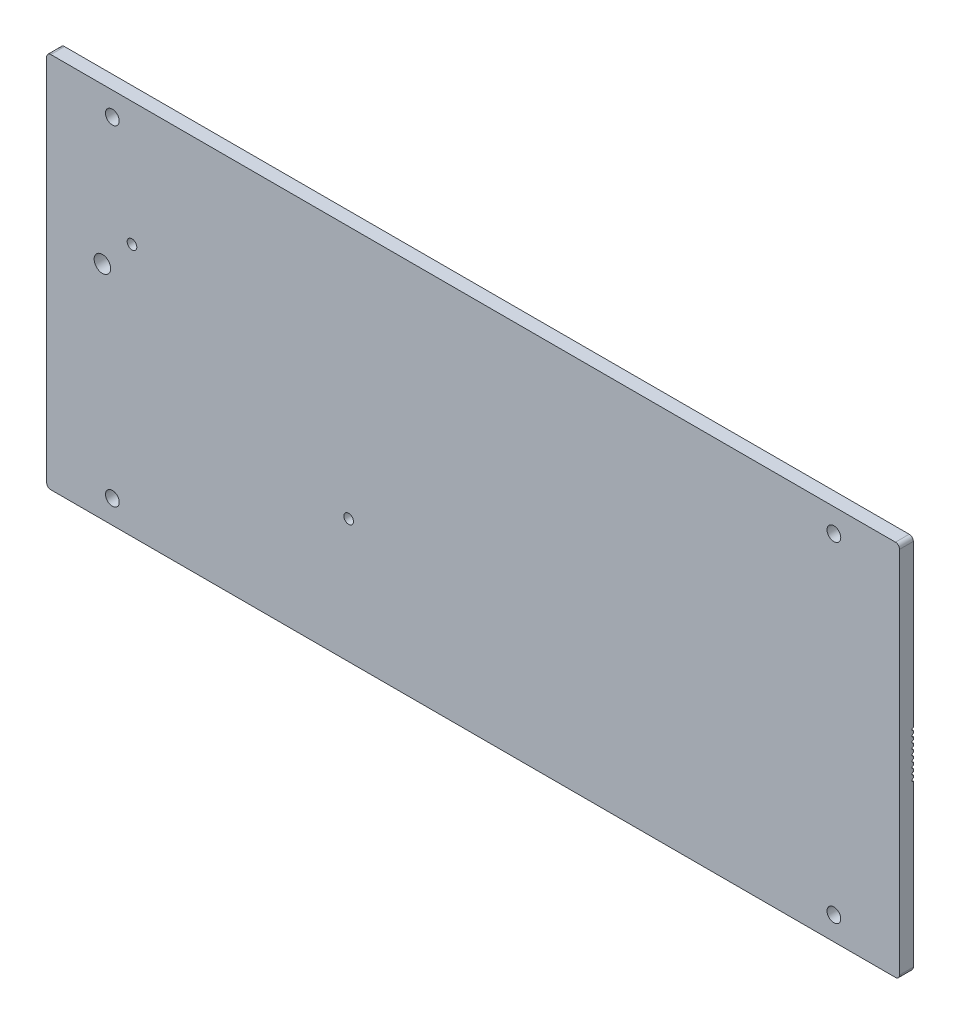
SolidWorks part; units mm, degrees
material "Alliage 1060"
ref_plane "Plan de face" through (0, 0, 0) normal (0, 0, 1) x (1, 0, 0)
ref_plane "Plan de dessus" through (0, 0, 0) normal (0, 1, 0) x (1, 0, 0)
ref_plane "Plan de droite" through (0, 0, 0) normal (1, 0, 0) x (0, 0, -1)
sketch "Esquisse1" plane through (0, 0, 0) normal (0, 0, 1) x (1, 0, 0)
  line L1 (-153.5, -68.5) -> (153.5, -68.5)
  line L2 (-155, -67) -> (-155, 67)
  line L3 (-153.5, 68.5) -> (153.5, 68.5)
  line L4 (155, -67) -> (155, 67)
  line L5 (-155, -68.5) -> (155, 68.5) construction
  line L6 (-155, 68.5) -> (155, -68.5) construction
  arc A0 (-153.5, -68.5) -> (-155, -67) centre (-153.5, -67) cw
  arc A1 (153.5, -68.5) -> (155, -67) centre (153.5, -67) ccw
  arc A2 (153.5, 68.5) -> (155, 67) centre (153.5, 67) cw
  arc A3 (-155, 67) -> (-153.5, 68.5) centre (-153.5, 67) cw
  point P0 (0, 0)
  dimension "D3" = 1.5
  dimension "D1" = 310
  dimension "D2" = 137
extrude "Boss.-Extru.1" add sketch "Esquisse1" along normal blind 5
ref_plane "Plan1" through (0, 0, 0) normal (0, -1, 0) x (-1, 0, 0)
sketch "Esquisse2" plane through (0, 0, 0) normal (0, 0, -1) x (-1, 0, 0)
  line L0 (-131.1192, -70) -> (-131.1192, -50) construction
  line L1 (-150, -70) -> (150, -70) construction
  line L2 (-155, 0) -> (155, 0) construction
  line L3 (-155, -67) -> (-155, 67) construction
  line L4 (155, 67) -> (155, -67) construction
  line L5 (0, 0) -> (0, 70) construction
  line L6 (-150, 70) -> (150, 70) construction
  circle A0 centre (-131.1192, -60) radius 2.5
  circle A1 centre (-131.1192, 60) radius 2.5
  circle A2 centre (131.1192, 60) radius 2.5
  circle A3 centre (131.1192, -60) radius 2.5
  dimension "D1" = 20
extrude "Enlèv. mat.-Extru.1" cut sketch "Esquisse2" against normal blind 5
sketch "Esquisse3" plane through (155, 0, 0) normal (1, 0, 0) x (0, 0, -1)
  circle A0 centre (0, 0) radius 0.5
  circle A1 centre (0, 2) radius 0.5
  circle A2 centre (0, 4) radius 0.5
  circle A3 centre (0, 6) radius 0.5
  circle A4 centre (0, 8) radius 0.5
  circle A5 centre (0, -2) radius 0.5
  circle A6 centre (0, -4) radius 0.5
  circle A7 centre (0, -6) radius 0.5
  circle A8 centre (0, -8) radius 0.5
  dimension "D1" = 5
  dimension "D2" = 5
extrude "Enlèv. mat.-Extru.2" cut sketch "Esquisse3" against normal through all both and the other way through all
sketch "Esquisse4" plane through (0, 0, 0) normal (0, 0, -1) x (-1, 0, 0)
  circle A0 centre (45.2359, -23.5) radius 1.75
  circle A1 centre (123.9859, 23.5) radius 1.75
extrude "Enlèv. mat.-Extru.3" cut sketch "Esquisse4" against normal blind 5
sketch "Esquisse6" plane through (0, 0, 0) normal (0, 0, -1) x (-1, 0, 0)
  circle A0 centre (134.7465, 11.9777) radius 3
extrude "Enlèv. mat.-Extru.4" cut sketch "Esquisse6" against normal blind 5
fillet "Congé1" radius 0.5 1 edges at (-137.7465, 11.9777, 0)
